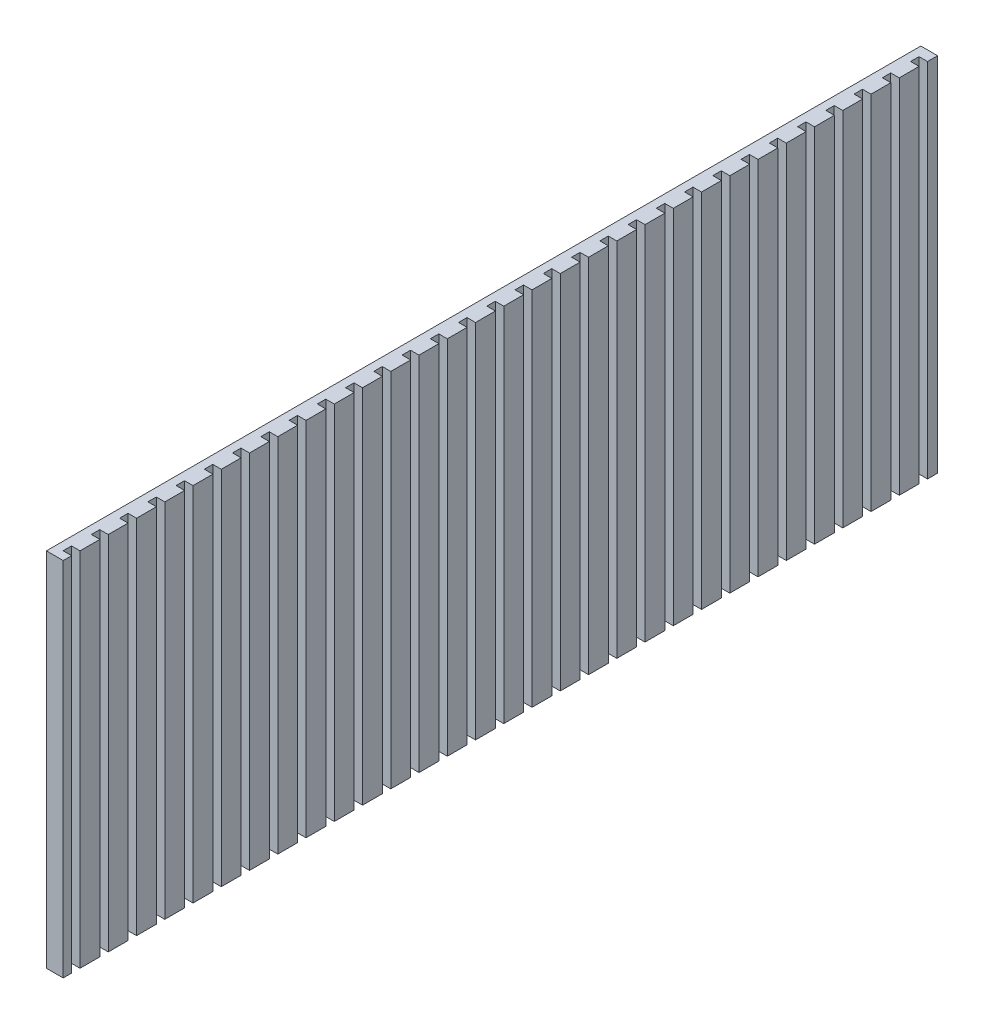
SolidWorks part; units mm, degrees
material "Free-Cutting Brass, UNS C36000"
ref_plane "Front Plane" through (0, 0, 0) normal (0, 0, 1) x (1, 0, 0)
ref_plane "Top Plane" through (0, 0, 0) normal (0, 1, 0) x (1, 0, 0)
ref_plane "Right Plane" through (0, 0, 0) normal (1, 0, 0) x (0, 0, -1)
sketch "Sketch1" plane through (0, 0, 0) normal (1, 0, 0) x (0, 0, -1)
  line L1 (-260, -107.5) -> (260, -107.5)
  line L2 (-260, -107.5) -> (-260, 107.5)
  line L3 (-260, 107.5) -> (260, 107.5)
  line L4 (260, -107.5) -> (260, 107.5)
  line L5 (-260, -107.5) -> (260, 107.5) construction
  line L6 (-260, 107.5) -> (260, -107.5) construction
  point P0 (0, 0)
  dimension "D1" = 520
  dimension "D2" = 215
extrude "Boss-Extrude1" add sketch "Sketch1" along normal blind 10
sketch "Sketch2" plane through (0, 107.5, 0) normal (0, 1, 0) x (1, 0, 0)
  line L0 (10, 260) -> (10, -260) construction
  line L1 (15.0659, -250) -> (4.9341, -250)
  line L2 (15.0659, -250) -> (15.0659, -255)
  line L3 (15.0659, -255) -> (4.9341, -255)
  line L4 (4.9341, -250) -> (4.9341, -255)
  line L5 (15.0659, -250) -> (4.9341, -255) construction
  line L6 (15.0659, -255) -> (4.9341, -250) construction
  line L7 (10, -260) -> (0, -260) construction
  point P0 (10, -252.5)
  dimension "D1" = 10.1318
  dimension "D2" = 5
  dimension "D3" = 5
extrude "Cut-Extrude1" cut sketch "Sketch2" against normal through all
pattern_linear "LPattern1" count 31 spacing 16.8 along (0, 0, -1) of "Cut-Extrude1"
